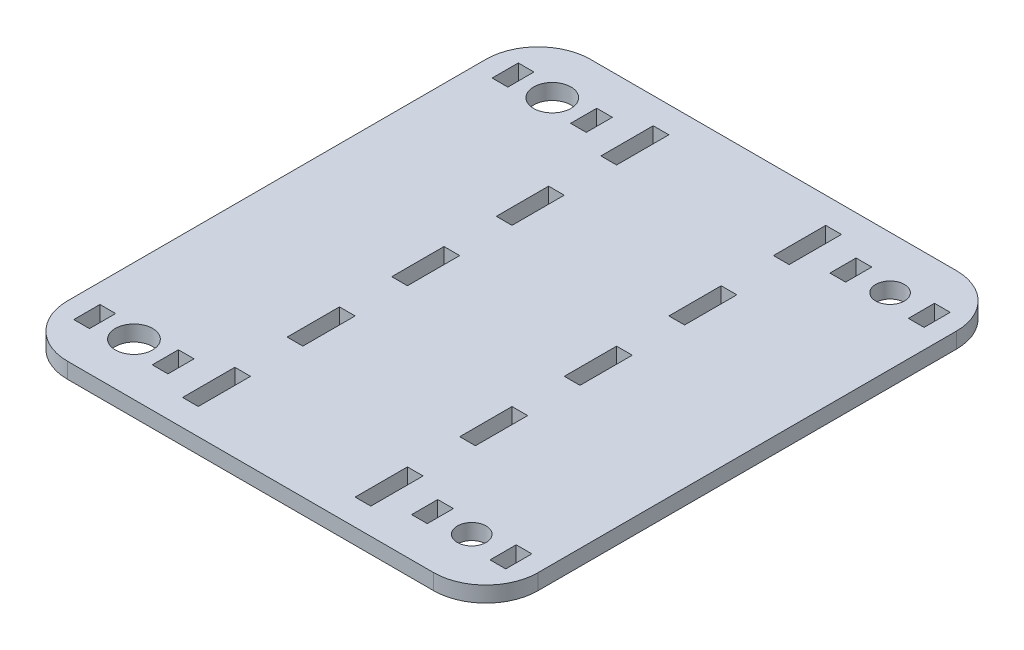
SolidWorks part; units mm, degrees
ref_plane "Front Plane" through (0, 0, 0) normal (0, 0, 1) x (1, 0, 0)
ref_plane "Top Plane" through (0, 0, 0) normal (0, 1, 0) x (1, 0, 0)
ref_plane "Right Plane" through (0, 0, 0) normal (1, 0, 0) x (0, 0, -1)
sketch "Sketch2" plane through (0, 0, 0) normal (0, 1, 0) x (1, 0, 0)
  line L0 (-45, 50) -> (-32.3, 50) construction
  line L1 (45, 50) -> (-45, 50)
  line L2 (45, 50) -> (45, -50)
  line L3 (45, -50) -> (-45, -50)
  line L4 (-45, 50) -> (-45, -50)
  line L5 (45, 50) -> (-45, -50) construction
  line L6 (45, -50) -> (-45, 50) construction
  line L7 (-32.3, 50) -> (-32.3, 40) construction
  line L8 (0, 0) -> (-50000, 0) construction
  line L9 (0, 0) -> (0, 50000) construction
  line L10 (38.3, 42.5) -> (41.3, 42.5)
  line L11 (0, 0) -> (-16.5, 0) construction
  line L12 (-15, 25) -> (-18, 25)
  line L13 (-15, 5) -> (-18, 5)
  line L14 (-15, 5) -> (-15, -5)
  line L15 (-15, -5) -> (-18, -5)
  line L16 (-18, 5) -> (-18, -5)
  line L17 (-15, 5) -> (-18, -5) construction
  line L18 (-15, -5) -> (-18, 5) construction
  line L19 (-15, 25) -> (-15, 15)
  line L20 (-15, 15) -> (-18, 15)
  line L21 (-18, 25) -> (-18, 15)
  line L22 (0, 20) -> (-16.5, 20) construction
  line L23 (-15, 25) -> (-18, 15) construction
  line L24 (-15, 15) -> (-18, 25) construction
  line L25 (-15, 45) -> (-18, 45)
  line L26 (-15, 45) -> (-15, 35)
  line L27 (-15, 35) -> (-18, 35)
  line L28 (-18, 45) -> (-18, 35)
  line L29 (0, 40) -> (-16.5, 40) construction
  line L30 (-15, 45) -> (-18, 35) construction
  line L31 (-15, 35) -> (-18, 45) construction
  line L32 (-15, -15) -> (-18, -15)
  line L33 (-15, -15) -> (-15, -25)
  line L34 (-15, -25) -> (-18, -25)
  line L35 (-18, -15) -> (-18, -25)
  line L36 (0, -20) -> (-16.5, -20) construction
  line L37 (-15, -15) -> (-18, -25) construction
  line L38 (-15, -25) -> (-18, -15) construction
  line L39 (-15, -35) -> (-18, -35)
  line L40 (-15, -35) -> (-15, -45)
  line L41 (-15, -45) -> (-18, -45)
  line L42 (-18, -35) -> (-18, -45)
  line L43 (0, -40) -> (-16.5, -40) construction
  line L44 (-15, -35) -> (-18, -45) construction
  line L45 (-15, -45) -> (-18, -35) construction
  line L46 (15, -45) -> (18, -35) construction
  line L47 (15, -35) -> (18, -45) construction
  line L48 (15, -25) -> (18, -15) construction
  line L49 (15, -15) -> (18, -25) construction
  line L50 (15, 35) -> (18, 45) construction
  line L51 (15, 45) -> (18, 35) construction
  line L52 (15, 15) -> (18, 25) construction
  line L53 (15, 25) -> (18, 15) construction
  line L54 (15, -5) -> (18, 5) construction
  line L55 (15, 5) -> (18, -5) construction
  line L56 (18, -35) -> (18, -45)
  line L57 (15, -45) -> (18, -45)
  line L58 (15, -35) -> (15, -45)
  line L59 (15, -35) -> (18, -35)
  line L60 (18, -15) -> (18, -25)
  line L61 (15, -25) -> (18, -25)
  line L62 (15, -15) -> (15, -25)
  line L63 (15, -15) -> (18, -15)
  line L64 (18, 45) -> (18, 35)
  line L65 (15, 35) -> (18, 35)
  line L66 (15, 45) -> (15, 35)
  line L67 (15, 45) -> (18, 45)
  line L68 (18, 25) -> (18, 15)
  line L69 (15, 15) -> (18, 15)
  line L70 (15, 25) -> (15, 15)
  line L71 (18, 5) -> (18, -5)
  line L72 (15, -5) -> (18, -5)
  line L73 (15, 5) -> (15, -5)
  line L74 (15, 5) -> (18, 5)
  line L75 (15, 25) -> (18, 25)
  line L76 (-32.3, 40) -> (-39.8, 40) construction
  line L77 (38.3, 37.5) -> (41.3, 37.5)
  line L78 (-38.3, 42.5) -> (-41.3, 42.5)
  line L79 (-38.3, 42.5) -> (-38.3, 37.5)
  line L80 (-38.3, 37.5) -> (-41.3, 37.5)
  line L81 (-41.3, 42.5) -> (-41.3, 37.5)
  line L82 (-38.3, 42.5) -> (-41.3, 37.5) construction
  line L83 (-38.3, 37.5) -> (-41.3, 42.5) construction
  line L84 (38.3, 42.5) -> (38.3, 37.5)
  line L85 (41.3, 42.5) -> (41.3, 37.5)
  line L86 (45, -50) -> (-45, 50) construction
  line L87 (41.3, -42.5) -> (41.3, -37.5)
  line L88 (38.3, -42.5) -> (38.3, -37.5)
  line L89 (38.3, -37.5) -> (41.3, -37.5)
  line L90 (38.3, -42.5) -> (41.3, -42.5)
  line L91 (-38.3, -37.5) -> (-41.3, -42.5) construction
  line L92 (-38.3, -42.5) -> (-41.3, -37.5) construction
  line L93 (-41.3, -42.5) -> (-41.3, -37.5)
  line L94 (-38.3, -37.5) -> (-41.3, -37.5)
  line L95 (-38.3, -42.5) -> (-38.3, -37.5)
  line L96 (-38.3, -42.5) -> (-41.3, -42.5)
  line L97 (-26.3, -42.5) -> (-26.3, -37.5)
  line L98 (-26.3, -37.5) -> (-23.3, -37.5)
  line L99 (-23.3, -42.5) -> (-23.3, -37.5)
  line L100 (-26.3, -42.5) -> (-23.3, -42.5)
  line L101 (-26.3, 37.5) -> (-23.3, 37.5)
  line L102 (-26.3, 42.5) -> (-26.3, 37.5)
  line L103 (-26.3, 42.5) -> (-23.3, 42.5)
  line L104 (-23.3, 42.5) -> (-23.3, 37.5)
  line L105 (32.3, -38.3165) -> (32.3, 49961.6835) construction
  line L106 (26.3, 42.5) -> (23.3, 42.5)
  line L107 (23.3, 42.5) -> (23.3, 37.5)
  line L108 (26.3, 42.5) -> (26.3, 37.5)
  line L109 (26.3, 37.5) -> (23.3, 37.5)
  line L110 (26.3, -37.5) -> (23.3, -37.5)
  line L111 (26.3, -42.5) -> (26.3, -37.5)
  line L112 (26.3, -42.5) -> (23.3, -42.5)
  line L113 (23.3, -42.5) -> (23.3, -37.5)
  circle A0 centre (-32.3, 40) radius 3.5685
  circle A1 centre (-32.3, -40) radius 3.5685
  circle A2 centre (32.3, 40) radius 2.75
  circle A3 centre (32.3, -40) radius 2.75
  point P0 (0, 0)
  dimension "D4" = 7.137
  dimension "D5" = 5.5
  dimension "D1" = 100
  dimension "D2" = 90
  dimension "D3" = 10
  dimension "D6" = 3
  dimension "D7" = 10
  dimension "D8" = 3
  dimension "D10" = 5
  dimension "D11" = 3
  dimension "D12" = 7.5
  dimension "D9" = 3
extrude "Boss-Extrude1" add sketch "Sketch2" along normal blind 3
fillet "Fillet1" radius 10 4 edges at (-45, 1.5, -50) (45, 1.5, -50) (45, 1.5, 50) (-45, 1.5, 50)
